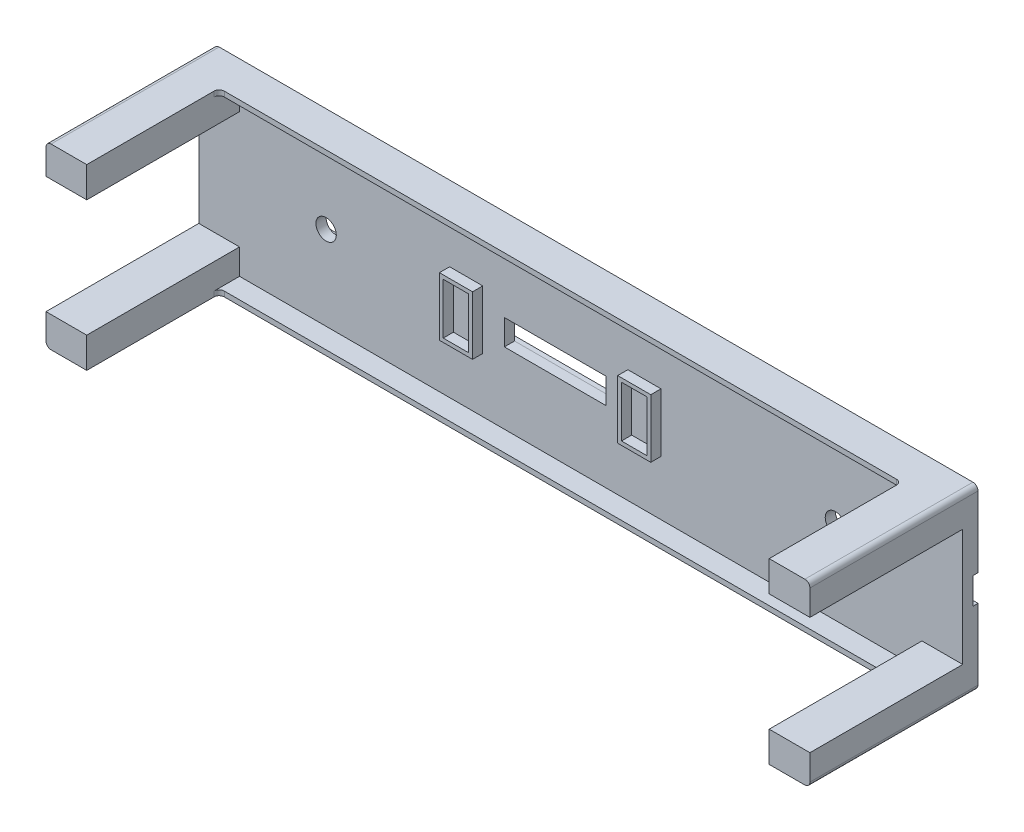
SolidWorks part; units mm, degrees
ref_plane "Přední rovina" through (0, 0, 0) normal (0, 0, 1) x (1, 0, 0)
ref_plane "Horní rovina" through (0, 0, 0) normal (0, 1, 0) x (1, 0, 0)
ref_plane "Pravá rovina" through (0, 0, 0) normal (1, 0, 0) x (0, 0, -1)
sketch "Skica1" plane through (0, 0, 0) normal (0, 0, 1) x (1, 0, 0)
  line L1 (75, 17.5) -> (-75, 17.5)
  line L2 (75, 17.5) -> (75, -17.5)
  line L3 (75, -17.5) -> (-75, -17.5)
  line L4 (-75, 17.5) -> (-75, -17.5)
  line L5 (75, 17.5) -> (-75, -17.5) construction
  line L6 (75, -17.5) -> (-75, 17.5) construction
  point P0 (0, 0)
  point P5 (-27.5, 0)
  point P11 (4.5, 0)
  dimension "D1" = 35
  dimension "D2" = 150
extrude "Přidat vysunutím2" add sketch "Skica1" along normal blind 3 contours L2 L1 L4 L3
sketch "Skica2" plane through (0, 0, 3) normal (0, 0, 1) x (1, 0, 0)
  line L0 (-75, 17.5) -> (-75, -17.5) construction
  line L1 (-25, 5) -> (-20, 5)
  line L2 (-25, 5) -> (-25, -5)
  line L3 (-25, -5) -> (-20, -5)
  line L4 (-20, 5) -> (-20, -5)
  line L5 (-25, 5) -> (-20, -5) construction
  line L6 (-25, -5) -> (-20, 5) construction
  line L8 (15, 5) -> (10, 5)
  line L9 (15, 5) -> (15, -5)
  line L10 (15, -5) -> (10, -5)
  line L11 (10, 5) -> (10, -5)
  line L12 (15, 5) -> (10, -5) construction
  line L13 (15, -5) -> (10, 5) construction
  line L14 (-25.75, 5.75) -> (-19.25, 5.75)
  line L15 (-25.75, 5.75) -> (-25.75, -5.75)
  line L16 (-25.75, -5.75) -> (-19.25, -5.75)
  line L17 (-19.25, 5.75) -> (-19.25, -5.75)
  line L18 (-25.75, 5.75) -> (-19.25, -5.75) construction
  line L19 (-25.75, -5.75) -> (-19.25, 5.75) construction
  line L20 (9.25, 5.75) -> (15.75, 5.75)
  line L21 (9.25, 5.75) -> (9.25, -5.75)
  line L22 (9.25, -5.75) -> (15.75, -5.75)
  line L23 (15.75, 5.75) -> (15.75, -5.75)
  line L24 (9.25, 5.75) -> (15.75, -5.75) construction
  line L25 (9.25, -5.75) -> (15.75, 5.75) construction
  point P0 (-22.5, 0)
  point P7 (12.5, 0)
  point P12 (-22.5, 0)
  point P17 (12.5, 0)
  dimension "D1" = 10
  dimension "D2" = 5
  dimension "D3" = 50
  dimension "D4" = 10
  dimension "D5" = 5
  dimension "D6" = 30
  dimension "D7" = 11.5
  dimension "D8" = 6.5
  dimension "D9" = 11.5
  dimension "D10" = 6.5
extrude "Přidat vysunutím3" add sketch "Skica2" along normal blind 2
sketch "Skica4" plane through (0, 0, 3) normal (0, 0, 1) x (1, 0, 0)
  line L0 (-19.25, -5.75) -> (-19.25, 5.75) construction
  line L1 (-15, 2.5) -> (5, 2.5)
  line L2 (-15, 2.5) -> (-15, -2.5)
  line L3 (-15, -2.5) -> (5, -2.5)
  line L4 (5, 2.5) -> (5, -2.5)
  line L5 (-15, 2.5) -> (5, -2.5) construction
  line L6 (-15, -2.5) -> (5, 2.5) construction
  line L7 (9.25, 5.75) -> (9.25, -5.75) construction
  point P0 (-5, 0)
  point P7 (-19.25, 0)
  dimension "D1" = 5
  dimension "D2" = 20
  dimension "D3" = 4.25
  dimension "D4" = 4.25
extrude "Odebrat vysunutím1" cut sketch "Skica4" against normal blind 2
sketch "Skica5" plane through (0, 0, 0) normal (0, 0, -1) x (-1, 0, 0)
  line L10 (75, 17.5) -> (75, -17.5) construction
  line L11 (-75, 2.6) -> (75, 2.6)
  line L12 (-75, 2.6) -> (-75, -2.6)
  line L13 (-75, -2.6) -> (75, -2.6)
  line L14 (75, 2.6) -> (75, -2.6)
  line L15 (-75, 2.6) -> (75, -2.6) construction
  line L16 (-75, -2.6) -> (75, 2.6) construction
  point P0 (0, 0)
  dimension "D1" = 5.2
extrude "Odebrat vysunutím3" cut sketch "Skica5" against normal blind 1 contours L11 L14 L13 L12
sketch "Skica7" plane through (0, 0, 1) normal (0, 0, -1) x (-1, 0, 0)
  circle A0 centre (-50, 0) radius 2
  circle A1 centre (50, 0) radius 2
  point P4 (0, 0)
  dimension "D1" = 4
  dimension "D2" = 50
  dimension "D3" = 50
extrude "Odebrat vysunutím4" cut sketch "Skica7" against normal through all
sketch "Skica8" plane through (0, 0, 3) normal (0, 0, 1) x (1, 0, 0)
  line L0 (0, 0) -> (0, -17.5) construction
  line L1 (75, 17.5) -> (67, 17.5)
  line L2 (75, 17.5) -> (75, 11.5)
  line L3 (75, 11.5) -> (67, 11.5)
  line L4 (67, 17.5) -> (67, 11.5)
  line L5 (75, -17.5) -> (67, -17.5)
  line L6 (75, -17.5) -> (75, -11.5)
  line L7 (75, -11.5) -> (67, -11.5)
  line L8 (67, -17.5) -> (67, -11.5)
  line L9 (75, -17.5) -> (-75, -17.5) construction
  line L10 (-67, -17.5) -> (-67, -11.5)
  line L11 (-75, -17.5) -> (-67, -17.5)
  line L12 (-75, -17.5) -> (-75, -11.5)
  line L13 (-75, -11.5) -> (-67, -11.5)
  line L14 (-75, 17.5) -> (-75, 11.5)
  line L15 (-75, 17.5) -> (-67, 17.5)
  line L16 (-67, 17.5) -> (-67, 11.5)
  line L17 (-75, 11.5) -> (-67, 11.5)
  dimension "D1" = 6
  dimension "D2" = 8
extrude "Přidat vysunutím4" add sketch "Skica8" along normal blind 30
fillet "Zaoblit1" radius 1 4 edges at (75, 17.5, 16.5) (75, -17.5, 16.5) (-75, 17.5, 16.5) (-75, -17.5, 16.5)
sketch "Skica9" plane through (0, 0, 3) normal (0, 0, 1) x (1, 0, 0)
  line L0 (-67, 11.5) -> (-67, 17.5) construction
  line L1 (67, 17.5) -> (-67, 17.5)
  line L2 (67, 17.5) -> (67, 16.5)
  line L3 (67, 16.5) -> (-67, 16.5)
  line L4 (-67, 17.5) -> (-67, 16.5)
  line L5 (67, -11.5) -> (67, -17.5) construction
  line L6 (-67, -17.5) -> (67, -17.5)
  line L7 (-67, -17.5) -> (-67, -16.5)
  line L8 (-67, -16.5) -> (67, -16.5)
  line L9 (67, -17.5) -> (67, -16.5)
  dimension "D1" = 1
  dimension "D2" = 1
extrude "Přidat vysunutím5" add sketch "Skica9" along normal blind 4
fillet "Zaoblit2" radius 1 4 edges at (-67, -17, 7) (67, -17, 7) (67, 17, 7) (-67, 17, 7)
